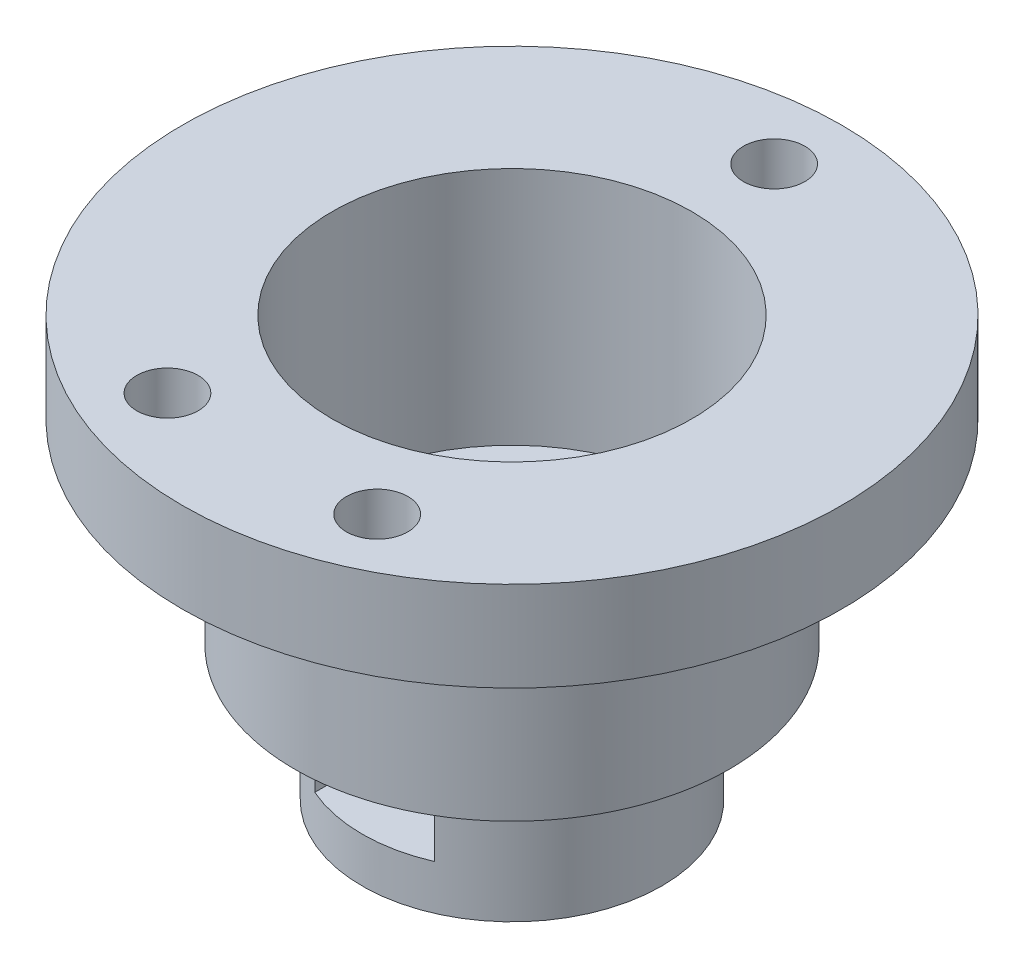
SolidWorks part; units mm, degrees
ref_plane "Front" through (0, 0, 0) normal (0, 0, 1) x (1, 0, 0)
ref_plane "Top" through (0, 0, 0) normal (0, 1, 0) x (1, 0, 0)
ref_plane "Right" through (0, 0, 0) normal (1, 0, 0) x (0, 0, -1)
sketch "Sketch1" plane through (0, 0, 0) normal (0, 1, 0) x (1, 0, 0)
  circle A0 centre (0, 0) radius 10
  dimension "D1" = 20
extrude "Boss-Extrude1" add sketch "Sketch1" along normal blind 9
sketch "Sketch2" plane through (0, 9, 0) normal (0, 1, 0) x (1, 0, 0)
  circle A0 centre (0, 0) radius 14.5
  dimension "D1" = 29
extrude "Boss-Extrude2" add sketch "Sketch2" along normal blind 3
sketch "Sketch3" plane through (0, 12, 0) normal (0, 1, 0) x (1, 0, 0)
  circle A0 centre (0, 0) radius 12
  circle A1 centre (0, 0) radius 14.5
  circle A2 centre (0, 0) radius 14.5
  dimension "D1" = 0
  dimension "D2" = 2.5
extrude "Boss-Extrude3" add sketch "Sketch3" along normal blind 10
sketch "Sketch4" plane through (0, 12, 0) normal (0, 1, 0) x (1, 0, 0)
  circle A0 centre (0, 0) radius 3
  dimension "D1" = 6
extrude "Cut-Extrude1" cut sketch "Sketch4" against normal through all
sketch "Sketch5" plane through (0, 0, 0) normal (0, -1, 0) x (1, 0, 0)
  line L0 (0, 0) -> (-13, 0) construction
  line L1 (-9.8869, 1.5) -> (-13, 1.5)
  line L2 (-9.8869, -1.5) -> (-13, -1.5)
  line L3 (0, 1.5) -> (-13, 1.5) construction
  line L4 (0, -1.5) -> (-13, -1.5) construction
  circle A0 centre (-13, 0) radius 1.5
  circle A1 centre (0, 0) radius 10 construction
  circle A2 centre (0, 0) radius 10
  circle M5 centre (0, 0) radius 10
  dimension "D2" = 3
  dimension "D1" = 13
  dimension "D3" = 1.5
  dimension "D4" = 1.5
extrude "Boss-Extrude4" add sketch "Sketch5" against normal up to next contours A0 | A0 L2 L1 M5
ref_plane "Plane2" through (0, 3, 0) normal (0, -1, 0) x (-1, 0, 0)
sketch "Sketch6" plane through (0, 3, 0) normal (0, -1, 0) x (-1, 0, 0)
  line L1 (4, 2.3094) -> (0, 4.6188)
  line L2 (0, 4.6188) -> (-4, 2.3094)
  line L3 (-4, 2.3094) -> (-4, -9.1652)
  line L6 (4, -9.1652) -> (4, 2.3094)
  line L7 (-4, -2.3094) -> (-2, -3.4641) [skipped]
  line L8 (2, -3.4641) -> (4, -2.3094) [skipped]
  circle A0 centre (0, 0) radius 4 construction
  arc A1 (9.8869, 1.5) -> (9.8869, -1.5) centre (0, 0) ccw construction
  arc A2 (9.8869, 1.5) -> (9.8869, -1.5) centre (0, 0) ccw
  dimension "D1" = 8
extrude "Cut-Extrude2" cut sketch "Sketch6" against normal blind 3.8 contours L3 A2 L6 L1 L2
sketch "Sketch7" plane through (0, 22, 0) normal (0, 1, 0) x (1, 0, 0)
  circle A0 centre (0, 0) radius 12 construction
  circle A1 centre (0, 0) radius 12
  circle A2 centre (0, 0) radius 22
  dimension "D1" = 44
extrude "Boss-Extrude5" add sketch "Sketch7" along normal blind 6
sketch "Sketch8" plane through (0, 28, 0) normal (0, 1, 0) x (1, 0, 0)
  circle A0 centre (0, 17.5) radius 2.05
  circle A1 centre (-7, -16) radius 2.05
  circle A2 centre (7, -16) radius 2.05
  dimension "D1" = 4.1
  dimension "D3" = 4.1
  dimension "D4" = 4.1
  dimension "D2" = 17.5
  dimension "D5" = 7
  dimension "D6" = 7
  dimension "D7" = 16
extrude "Cut-Extrude3" cut sketch "Sketch8" against normal blind 5
